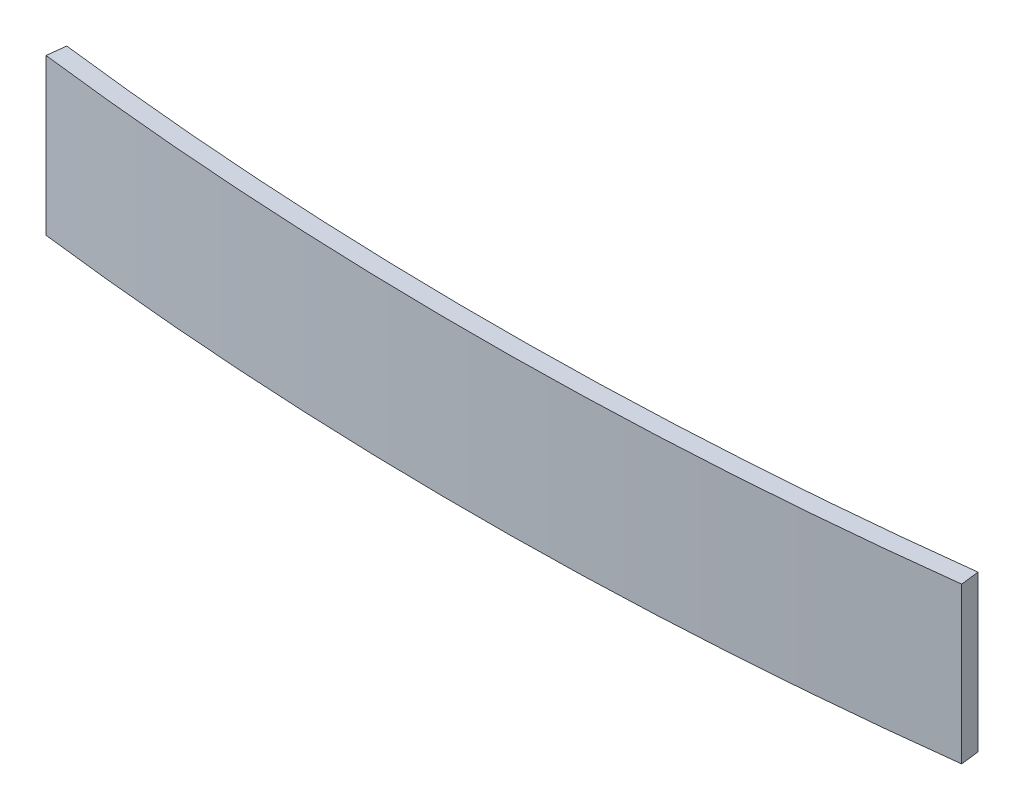
SolidWorks part; units mm, degrees
ref_plane "Front Plane" through (0, 0, 0) normal (0, 0, 1) x (1, 0, 0)
ref_plane "Top Plane" through (0, 0, 0) normal (0, 1, 0) x (1, 0, 0)
ref_plane "Right Plane" through (0, 0, 0) normal (1, 0, 0) x (0, 0, -1)
sketch "Sketch2" plane through (0, 0, 0) normal (0, 1, 0) x (1, 0, 0)
  line L3 (-73.1153, 2.6297) -> (-72.7519, 5.6076)
  line L4 (73.8847, 2.6297) -> (73.5213, 5.6076)
  arc A0 (-73.1153, 2.6297) -> (73.8847, 2.6297) centre (0.3847, 604.9793) ccw
  arc A1 (-72.7519, 5.6076) -> (73.5213, 5.6076) centre (0.3847, 604.9793) ccw
  dimension "D2" = 147
  dimension "D1" = 3
extrude "Boss-Extrude1" add sketch "Sketch2" along normal blind 25
